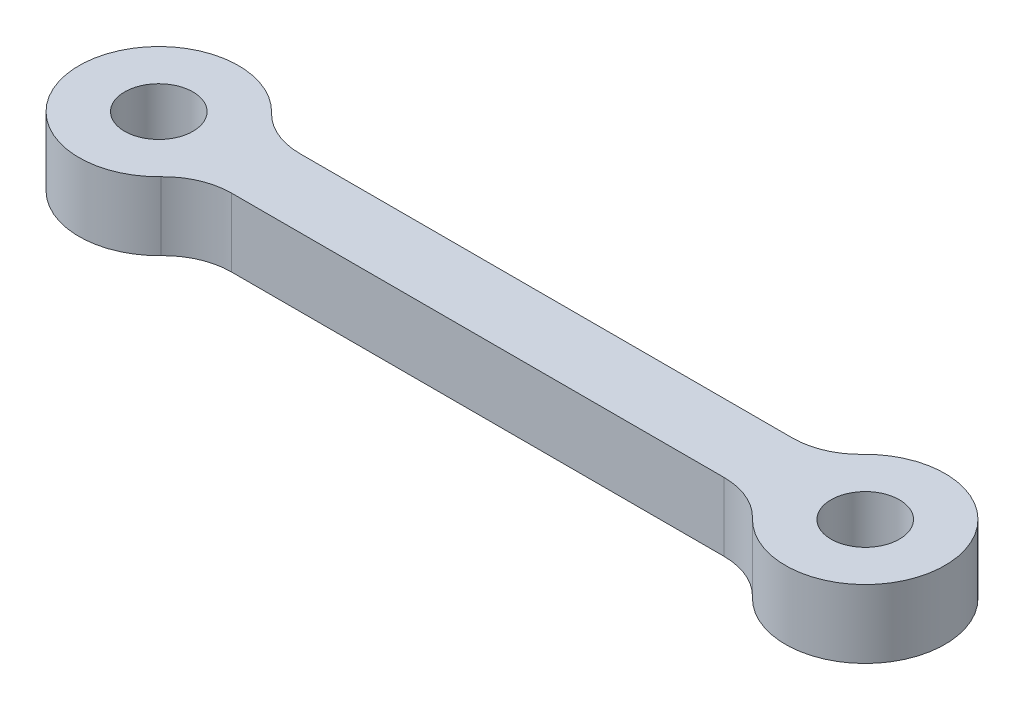
SolidWorks part; units mm, degrees
ref_plane "Front" through (0, 0, 0) normal (0, 0, 1) x (1, 0, 0)
ref_plane "Top" through (0, 0, 0) normal (0, 1, 0) x (1, 0, 0)
ref_plane "Right" through (0, 0, 0) normal (1, 0, 0) x (0, 0, -1)
sketch "Sketch1" plane through (0, 0, 0) normal (0, 1, 0) x (1, 0, 0)
  line L1 (-12.3377, -1.5) -> (12.3377, -1.5)
  line L3 (-12.3377, 1.5) -> (12.3377, 1.5)
  line L5 (-15.5, -1.5) -> (15.5, 1.5) construction
  line L6 (-15.5, 1.5) -> (15.5, -1.5) construction
  circle A0 centre (15.5, 0) radius 3.5
  circle A1 centre (15.5, 0) radius 1.5
  circle A2 centre (-15.5, 0) radius 1.5
  circle A3 centre (-15.5, 0) radius 3.5
  point P0 (0, 0)
  dimension "D1" = 7
  dimension "D2" = 3
  dimension "D3" = 7
  dimension "D4" = 3
  dimension "D5" = 31
  dimension "D7" = 1.5
  dimension "D6" = 3
  dimension "D8" = 15.5
extrude "Boss-Extrude1" add sketch "Sketch1" along normal mid plane 3 contours A3 L1 A0 L3 | A3 A2 | A0 A1
fillet "Fillet1" radius 3 4 edges at (-12.3377, 0, -1.5) (12.3377, 0, -1.5) (12.3377, 0, 1.5) (-12.3377, 0, 1.5)
